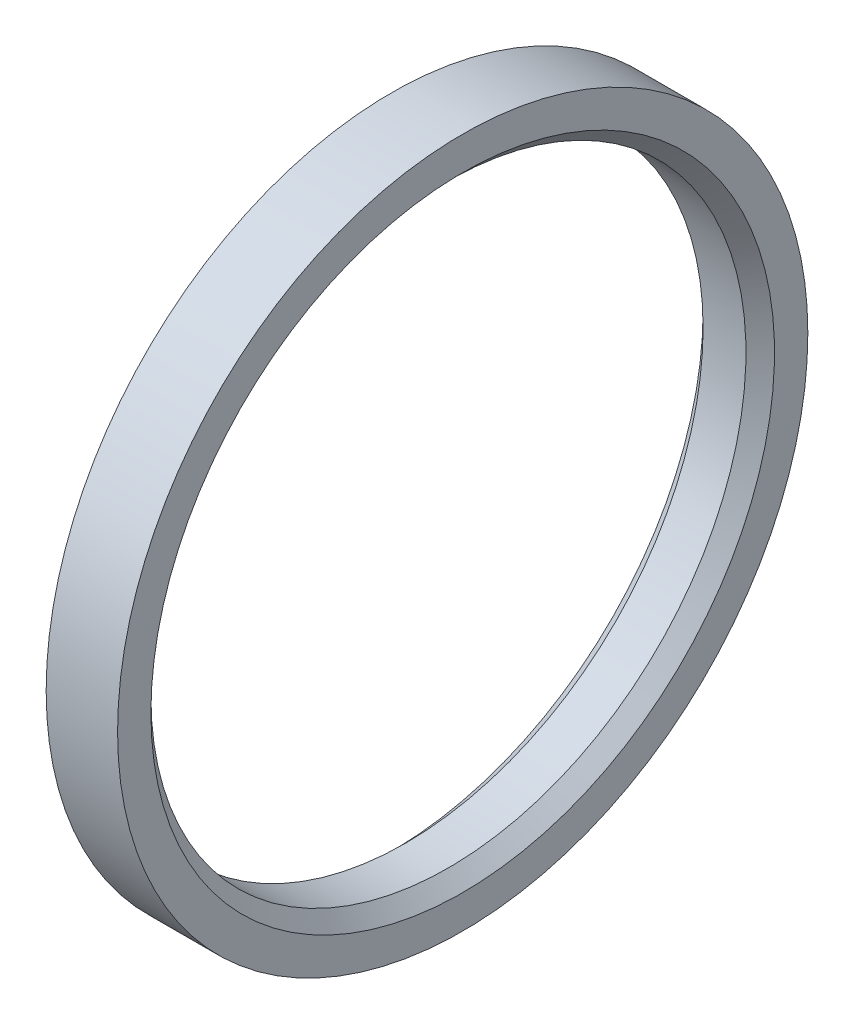
SolidWorks part; units mm, degrees
material "1060 Сплав"
ref_plane "Спереди" through (0, 0, 0) normal (0, 0, 1) x (1, 0, 0)
ref_plane "Сверху" through (0, 0, 0) normal (0, 1, 0) x (1, 0, 0)
ref_plane "Справа" through (0, 0, 0) normal (1, 0, 0) x (0, 0, -1)
sketch "Эскиз1" plane through (0, 0, 0) normal (0, 0, 1) x (1, 0, 0)
  line L0 (0, 0) -> (21971.9122, 0) construction
  line L1 (0, 14.5) -> (0, 12.5)
  line L2 (0, 12.5) -> (3, 12.5)
  line L3 (3, 12.5) -> (3, 14.5)
  line L4 (3, 14.5) -> (0, 14.5)
  dimension "D1" = 25
  dimension "D2" = 3
  dimension "D3" = 2
revolve "Повернуть1" add sketch "Эскиз1" angle 360 about L0
chamfer "Фаска1" distance 0.6 angle 45 2 edges at (3, 0, 12.5) (0, 0, 12.5)
